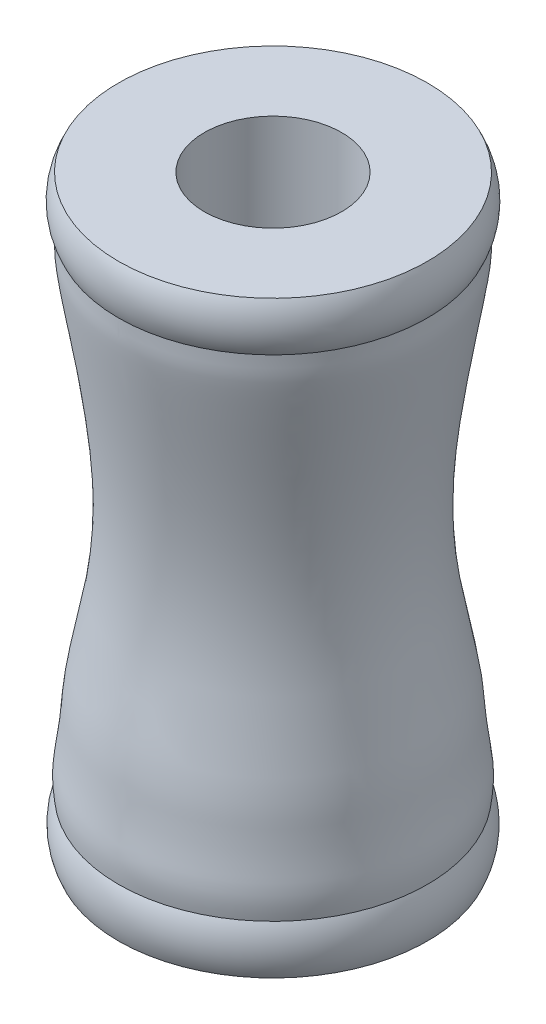
SolidWorks part; units mm, degrees
ref_plane "前视基准面" through (0, 0, 0) normal (0, 0, 1) x (1, 0, 0)
ref_plane "上视基准面" through (0, 0, 0) normal (0, 1, 0) x (1, 0, 0)
ref_plane "右视基准面" through (0, 0, 0) normal (1, 0, 0) x (0, 0, -1)
sketch "草图1" plane through (0, 0, 0) normal (1, 0, 0) x (0, 0, -1)
  line L0 (0, 0) -> (0, -11.3274) construction
  line L1 (1.4, 4.5977) -> (1.4, -5.4023)
  line L2 (1.4, 4.5977) -> (3.15, 4.5977) construction
  line L3 (1.4, -5.4023) -> (3.15, -5.4023) construction
  line L4 (1.4, 4.5977) -> (1.4, 5.5977)
  line L5 (1.4, 5.5977) -> (3.15, 5.5977)
  line L6 (1.4, -5.4023) -> (1.4, -6.4023)
  line L7 (1.4, -6.4023) -> (3.15, -6.4023)
  arc A0 (3.15, 5.5977) -> (3.15, 4.5977) centre (2.1765, 5.0977) cw
  arc A2 (3.15, -5.4023) -> (3.15, -6.4023) centre (2.0705, -5.9023) cw
  spline S0 degree 3 poles (3.15, 4.5977) (3.1475, 4.3516) (3.1651, 4.1569) (2.9703, 3.0694) (2.5486, 0.5528) (2.577, -1.4639) (3.0119, -3.2042) (3.1102, -4.7701) (3.2274, -4.8425) (3.15, -5.4023) knots 0 0 0 0 0.064612 0.225246 0.398626 0.622834 0.743358 0.781075 1 1 1 1
  dimension "D1" = 10
  dimension "D2" = 1.4
  dimension "D3" = 3.15
  dimension "D4" = 3.15
  dimension "D5" = 1
  dimension "D6" = 1
revolve "旋转1" add sketch "草图1" angle 360 about L0
